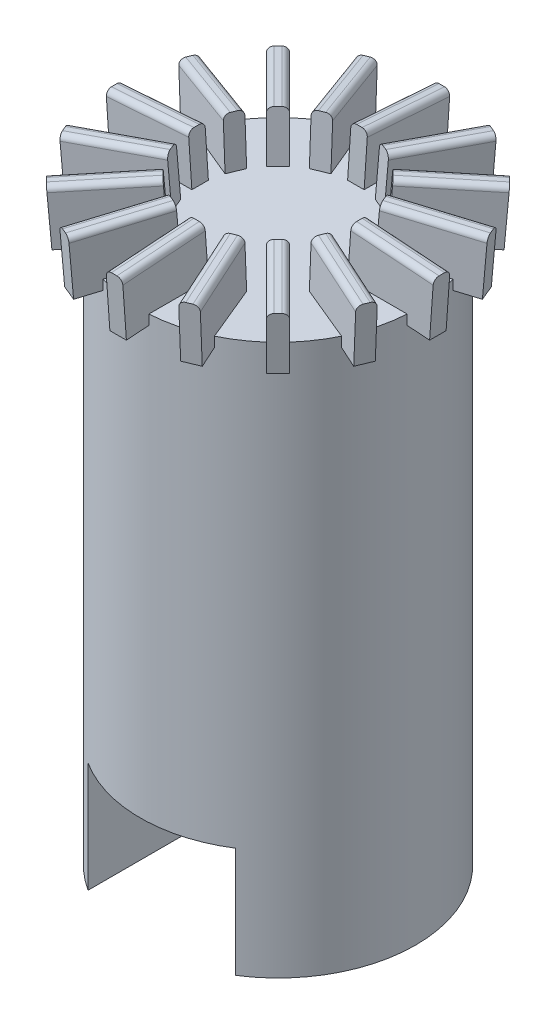
SolidWorks part; units mm, degrees
ref_plane "前视基准面" through (0, 0, 0) normal (0, 0, 1) x (1, 0, 0)
ref_plane "上视基准面" through (0, 0, 0) normal (0, 1, 0) x (1, 0, 0)
ref_plane "右视基准面" through (0, 0, 0) normal (1, 0, 0) x (0, 0, -1)
sketch "草图1" plane through (0, 0, 0) normal (0, 1, 0) x (1, 0, 0)
  circle A0 centre (0, 0) radius 5
  dimension "D1" = 10
extrude "凸台-拉伸1" add sketch "草图1" along normal blind 20
sketch "草图2" plane through (0, 20, 0) normal (0, 1, 0) x (1, 0, 0)
  line L0 (0, -5) -> (0, 5) construction
  circle A0 centre (0, 0) radius 5 construction
ref_plane "基准面1" through (1.4231, 19.8982, 0) normal (0.0713, 0.9975, 0) x (0, 0, -1)
sketch "草图3" plane through (1.4231, 19.8982, 0) normal (0.0713, 0.9975, 0) x (0, 0, -1)
  line L1 (-0.3, -4.3949) -> (0.3, -4.3949)
  line L2 (-0.3, -4.3949) -> (-0.3, -1.3949)
  line L3 (-0.3, -1.3949) -> (0.3, -1.3949)
  line L4 (0.3, -4.3949) -> (0.3, -1.3949)
  line L5 (-0.3, -4.3949) -> (0.3, -1.3949) construction
  line L6 (-0.3, -1.3949) -> (0.3, -4.3949) construction
  point P0 (0, -2.8949)
  dimension "D1" = 0.6
  dimension "D2" = 0
  dimension "D3" = 3
extrude "凸台-拉伸2" add sketch "草图3" along normal blind 2
fillet "圆角1" radius 0.2 2 edges at (4.4533, 21.6866, 0.3) (4.4533, 21.6866, -0.3)
pattern_circular "阵列(圆周)3" count 16 over 360 about axis through (0, 0, 0) along (0, 1, 0) of "凸台-拉伸2", "圆角1"
sketch "草图4" plane through (0, 0, 0) normal (0, -1, 0) x (-1, 0, 0)
  line L1 (2.6766, -5.7642) -> (-2.6766, -5.7642)
  line L2 (2.6766, -5.7642) -> (2.6766, 5.7642)
  line L3 (2.6766, 5.7642) -> (-2.6766, 5.7642)
  line L4 (-2.6766, -5.7642) -> (-2.6766, 5.7642)
  line L5 (2.6766, -5.7642) -> (-2.6766, 5.7642) construction
  line L6 (2.6766, 5.7642) -> (-2.6766, -5.7642) construction
  point P0 (0, 0)
extrude "切除-拉伸1" cut sketch "草图4" against normal blind 4
